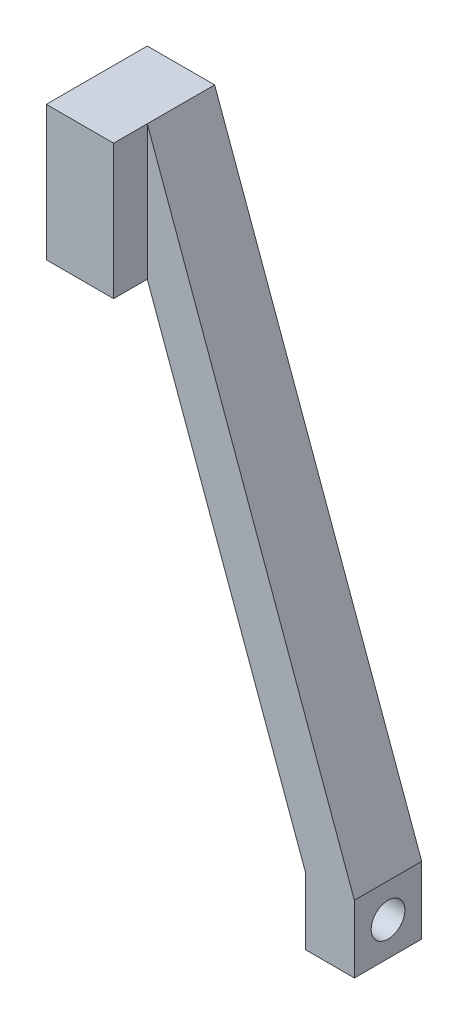
SolidWorks part; units mm, degrees
ref_plane "Front Plane" through (0, 0, 0) normal (0, 0, 1) x (1, 0, 0)
ref_plane "Top Plane" through (0, 0, 0) normal (0, 1, 0) x (1, 0, 0)
ref_plane "Right Plane" through (0, 0, 0) normal (1, 0, 0) x (0, 0, -1)
sketch "Sketch1" plane through (0, 0, 0) normal (0, 0, 1) x (1, 0, 0)
  line L0 (0, 0) -> (0, 25.4)
  line L1 (0, 25.4) -> (12.7, 25.4)
  line L2 (0, 0) -> (12.7, 0)
  line L3 (12.7, 0) -> (42.5092, -81.9)
  line L4 (42.5092, -94.6) -> (51.754, -94.6)
  line L5 (51.754, -94.6) -> (51.754, -81.9)
  line L6 (42.5092, -81.9) -> (42.5092, -94.6)
  line L7 (51.754, -81.9) -> (12.7, 25.4)
  dimension "D1" = 25.4
  dimension "D2" = 120
  dimension "D3" = 12.7
  dimension "D4" = 70
  dimension "D5" = 12.7
  dimension "D6" = 12.7
extrude "Boss-Extrude1" add sketch "Sketch1" against normal blind 12.7
sketch "Sketch2" plane through (42.5092, 0, 0) normal (-1, 0, 0) x (0, 0, 1)
  line L1 (-12.7, -81.9) -> (-12.7, -94.6) construction
  line L2 (-12.7, -81.9) -> (0, -81.9) construction
  circle A1 centre (-6.35, -88.25) radius 3.175
  point P4 (-12.7, -88.25)
  point P7 (-6.35, -81.9)
  dimension "D1" = 3.175
extrude "Cut-Extrude1" cut sketch "Sketch2" against normal through all
sketch "Sketch5" plane through (0, 0, -12.7) normal (0, 0, 1) x (1, 0, 0)
  line L0 (12.7, 25.4) -> (0, 25.4)
  line L1 (0, 25.4) -> (0, 0)
  line L2 (0, 0) -> (12.7, 0)
  line L4 (12.7, 0) -> (12.7, 25.4)
  line L5 (12.7, 0) -> (42.5092, -81.9) construction
extrude "Boss-Extrude2" add sketch "Sketch5" against normal blind 6.35
sketch "Sketch4" plane through (0, 0, 0) normal (0, -1, 0) x (1, 0, 0)
  line L0 (0, -12.7) -> (12.7, -12.7) construction
  line L3 (42.5092, -12.7) -> (42.5092, 0) construction
  circle A0 centre (6.35, -12.7) radius 3.175
  point P4 (6.35, -12.7)
  point P8 (42.5092, -6.35)
  dimension "D1" = 6.35
  dimension "D2" = 6.35
extrude "Cut-Extrude2" cut sketch "Sketch4" against normal blind 19.05
mirror "Mirror2" about plane through (42.5092, 0, 0) normal (0, 0, -1) of "Boss-Extrude1", "Cut-Extrude1", "Boss-Extrude2", "Cut-Extrude2"
sketch "Sketch6" plane through (0, 0, 0) normal (0, 0, 1) x (1, 0, 0)
  line L0 (12.7, 25.4) -> (0, 25.4) construction
  line L1 (0, 25.4) -> (0, 0) construction
  line L2 (0, 0) -> (12.7, 0) construction
  line L3 (12.7, 0) -> (42.5092, -81.9) construction
  line L4 (51.754, -81.9) -> (12.7, 25.4) construction
  line L5 (51.754, -94.6) -> (51.754, -81.9) construction
  line L6 (42.5092, -81.9) -> (42.5092, -94.6) construction
  line L7 (42.5092, -94.6) -> (51.754, -94.6) construction
  line L8 (12.7, 25.4) -> (0, 25.4)
  line L9 (0, 25.4) -> (0, 0)
  line L10 (0, 0) -> (12.7, 0)
  line L11 (12.7, 0) -> (42.5092, -81.9)
  line L12 (51.754, -81.9) -> (12.7, 25.4)
  line L13 (51.754, -94.6) -> (51.754, -81.9)
  line L14 (42.5092, -81.9) -> (42.5092, -94.6)
  line L15 (42.5092, -94.6) -> (51.754, -94.6)
extrude "Cut-Extrude3" cut sketch "Sketch6" against normal through all
